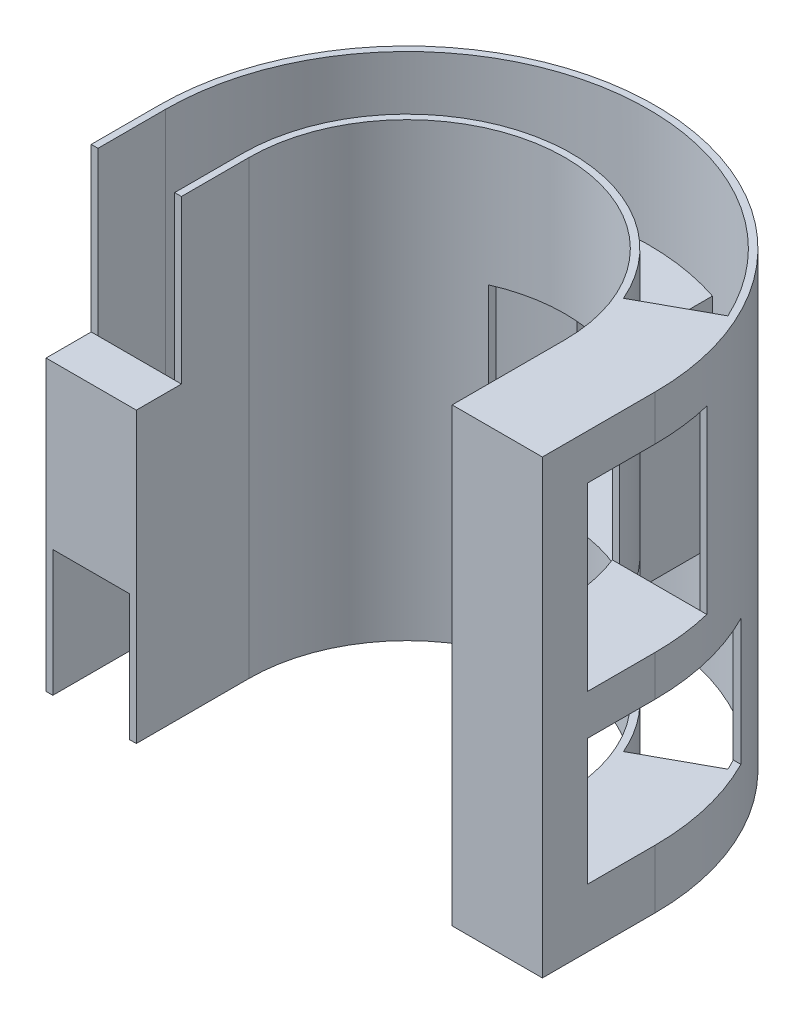
SolidWorks part; units mm, degrees
ref_plane "Front Plane" through (0, 0, 0) normal (0, 0, 1) x (1, 0, 0)
ref_plane "Top Plane" through (0, 0, 0) normal (0, 1, 0) x (1, 0, 0)
ref_plane "Right Plane" through (0, 0, 0) normal (1, 0, 0) x (0, 0, -1)
sketch "Sketch2" plane through (0, 0, 0) normal (0, 1, 0) x (1, 0, 0)
  circle A0 centre (0, 0) radius 27.5
  dimension "D1" = 55
extrude "Boss-Extrude1" add sketch "Sketch2" along normal blind 50 contours A0
sketch "Sketch3" plane through (0, 50, 0) normal (0, 1, 0) x (1, 0, 0)
  circle A0 centre (0, 0) radius 26.75
  dimension "D1" = 53.5
extrude "Cut-Extrude1" cut sketch "Sketch3" against normal through all
sketch "Sketch7" plane through (0, 50, 0) normal (0, 1, 0) x (1, 0, 0)
  circle A0 centre (0, 0) radius 18.25
  dimension "D1" = 36.5
extrude "Boss-Extrude3" add sketch "Sketch7" against normal blind 50 separate body
sketch "Sketch8" plane through (0, 50, 0) normal (0, 1, 0) x (1, 0, 0)
  circle A0 centre (0, 0) radius 17.5
  dimension "D1" = 35
extrude "Cut-Extrude3" cut sketch "Sketch8" against normal through all
sketch "Sketch9" plane through (0, 50, 0) normal (0, 1, 0) x (1, 0, 0)
  line L1 (-30.4577, 0) -> (29.5035, 0)
  line L2 (-30.4577, 0) -> (-30.4577, -28.5161)
  line L3 (-30.4577, -28.5161) -> (29.5035, -28.5161)
  line L4 (29.5035, 0) -> (29.5035, -28.5161)
extrude "Cut-Extrude4" cut sketch "Sketch9" against normal through all
sketch "Sketch10" plane through (0, 50, 0) normal (0, 1, 0) x (1, 0, 0)
  line L0 (-27.5, 0) -> (-27.5, -12.5)
  line L1 (-26.75, 0) -> (-27.5, 0) construction
  line L2 (-26.75, 0) -> (-26.75, -12.5)
  line L3 (-26.75, -12.5) -> (-27.5, -12.5)
  line L4 (-27.5, 0) -> (-26.75, 0)
  line L10 (-18.25, 0) -> (-17.5, 0)
  line L11 (-17.5, 0) -> (-18.25, 0) construction
  line L12 (-17.5, 0) -> (-17.5, -12.5)
  line L13 (-17.5, -12.5) -> (-18.25, -12.5)
  line L14 (-18.25, -12.5) -> (-18.25, 0)
  line L15 (17.5, 0) -> (18.25, 0)
  line L16 (18.25, 0) -> (18.25, -12.5)
  line L17 (18.25, -12.5) -> (17.5, -12.5)
  line L18 (17.5, -12.5) -> (17.5, 0)
  line L19 (27.5, 0) -> (26.75, 0)
  line L20 (26.75, 0) -> (26.75, -12.5)
  line L21 (26.75, -12.5) -> (27.5, -12.5)
  line L22 (27.5, -12.5) -> (27.5, 0)
  arc A0 (27.5, 0) -> (-27.5, 0) centre (0, 0) ccw construction
  arc A2 (17.5, 0) -> (-17.5, 0) centre (0, 0) ccw construction
  arc A3 (18.25, 0) -> (-18.25, 0) centre (0, 0) ccw construction
  dimension "D1" = 12.5
  dimension "D2" = 12.5
  dimension "D3" = 12.5
  dimension "D4" = 12.5
extrude "Boss-Extrude4" add sketch "Sketch10" against normal blind 50
sketch "Sketch11" plane through (0, 50, 0) normal (0, 1, 0) x (1, 0, 0)
  line L16 (18.25, -12.5) -> (18.25, 0) construction
  line L17 (16.7607, 7.2208) -> (24.2364, 11.3207)
  line L18 (18.25, 0) -> (18.25, -12.5)
  line L19 (18.25, -12.5) -> (26.75, -12.5)
  line L20 (26.75, -12.5) -> (26.75, 0)
  arc A4 (18.25, 0) -> (16.7607, 7.2208) centre (0, 0) ccw
  arc A5 (18.25, 0) -> (-18.25, 0) centre (0, 0) ccw construction
  arc A6 (26.75, 0) -> (24.2364, 11.3207) centre (0, 0) ccw
extrude "Boss-Extrude5" add sketch "Sketch11" against normal blind 5
sketch "Sketch12" plane through (27.5, 0, 0) normal (1, 0, 0) x (0, 0, -1)
  line L0 (-7.5, 45) -> (-7.5, 25)
  line L1 (-7.5, 25) -> (6.5, 25)
  line L2 (6.5, 25) -> (6.5, 45)
  line L3 (6.5, 45) -> (-7.5, 45)
  line L4 (-12.5, 0) -> (-12.5, 50) construction
  line L5 (27.5, 50) -> (0, 50) construction
  line L6 (-7.5, 20.5) -> (-7.5, 6.5)
  line L7 (-7.5, 6.5) -> (12.5, 6.5)
  line L8 (12.5, 6.5) -> (12.5, 20.5)
  line L9 (12.5, 20.5) -> (-7.5, 20.5)
  line L10 (-12.5, 0) -> (0, 0) construction
  dimension "D1" = 20
  dimension "D2" = 14
  dimension "D3" = 5
  dimension "D4" = 5
  dimension "D5" = 14
  dimension "D6" = 20
  dimension "D7" = 6.5
sketch "Sketch13" plane through (0, 0, 0) normal (0, -1, 0) x (1, 0, 0)
  line L0 (24.2364, -11.3207) -> (16.7607, -7.2208) construction
  line L1 (18.25, 0) -> (18.25, 12.5)
  line L2 (18.25, 12.5) -> (26.75, 12.5)
  line L3 (26.75, 12.5) -> (26.75, 0)
  line L4 (16.7607, -7.2208) -> (24.2364, -11.3207)
  arc A0 (18.25, 0) -> (16.7607, -7.2208) centre (0, 0) cw
  arc A3 (24.2364, -11.3207) -> (26.75, 0) centre (0, 0) ccw
  arc A4 (-26.75, 0) -> (26.75, 0) centre (0, 0) ccw construction
extrude "Boss-Extrude6" add sketch "Sketch13" against normal blind 6.5
extrude "Cut-Extrude6" cut sketch "Sketch12" against normal blind 15
sketch "Sketch14" plane through (0, 0, 12.5) normal (0, 0, 1) x (1, 0, 0)
  line L0 (7, 35) -> (7, 15)
  line L1 (7, 15) -> (-7, 15)
  line L2 (-7, 15) -> (-7, 35)
  line L3 (-7, 35) -> (7, 35)
  line L4 (17.5, 50) -> (-17.5, 50) construction
  dimension "D1" = 7
  dimension "D2" = 14
  dimension "D3" = 20
  dimension "D4" = 15
extrude "Cut-Extrude7" cut sketch "Sketch14" against normal blind 45
sketch "Sketch15" plane through (-27.5, 0, 0) normal (-1, 0, 0) x (0, 0, 1)
  line L0 (0, 0) -> (12.5, 0) construction
  line L1 (7.5, 54.2356) -> (24.1059, 54.2356)
  line L2 (7.5, 54.2356) -> (7.5, 32)
  line L3 (7.5, 32) -> (24.1059, 32)
  line L4 (24.1059, 54.2356) -> (24.1059, 32)
  line L5 (12.5, 0) -> (12.5, 50) construction
  dimension "D1" = 32
  dimension "D2" = 5
extrude "Cut-Extrude8" cut sketch "Sketch15" against normal blind 15
sketch "Sketch17" plane through (0, 25, 0) normal (0, 1, 0) x (1, 0, 0)
  line L0 (16.2481, 6.5) -> (17.0532, 6.5) construction
  line L1 (25.9483, 6.5) -> (26.7208, 6.5) construction
  line L2 (26.7208, 6.5) -> (17.0532, 6.5)
  line L3 (27.5, 0) -> (27.5, -7.5)
  line L4 (27.5, -7.5) -> (18.25, -7.5)
  line L5 (18.25, -7.5) -> (18.25, 0)
  arc A0 (18.25, 0) -> (17.0532, 6.5) centre (0, 0) ccw
  arc A1 (27.5, 0) -> (26.7208, 6.5) centre (0, 0) ccw
extrude "Boss-Extrude8" add sketch "Sketch17" against normal blind 4.5
sketch "Sketch18" plane through (0, 35, 0) normal (0, -1, 0) x (1, 0, 0)
  line L0 (7, -26.5942) -> (7, -25.8179) construction
  line L1 (-7, -16.8542) -> (-7, -25.8179)
  line L2 (7, -16.8542) -> (7, -25.8179)
  arc A0 (-7, -16.8542) -> (7, -16.8542) centre (0, 0) ccw
  arc A1 (-7, -16.8542) -> (7, -16.8542) centre (0, 0) ccw construction
  arc A2 (-7, -25.8179) -> (7, -25.8179) centre (0, 0) ccw
extrude "Boss-Extrude9" add sketch "Sketch18" against normal blind 2
sketch "Sketch19" plane through (0, 15, 0) normal (0, 1, 0) x (1, 0, 0)
  line L0 (7, 16.8542) -> (7, 16.039) construction
  line L1 (7, 25.8179) -> (7, 16.8542)
  line L2 (-7, 25.8179) -> (-7, 16.8542)
  arc A0 (-7, 16.8542) -> (7, 16.8542) centre (0, 0) cw
  arc A1 (-7, 25.8179) -> (7, 25.8179) centre (0, 0) cw
  arc A2 (7, 25.8179) -> (-7, 25.8179) centre (0, 0) ccw construction
extrude "Boss-Extrude10" add sketch "Sketch19" against normal blind 2
sketch "Sketch24" plane through (0, 37, 0) normal (0, 1, 0) x (1, 0, 0)
  line L0 (8.4749, 25.372) -> (8.4749, 16.1629)
  line L1 (7, 25.8179) -> (7, 16.8542)
  arc A1 (7, 25.8179) -> (8.4749, 25.372) centre (0, 0) cw
  arc A3 (7, 16.8542) -> (8.4749, 16.1629) centre (0, 0) cw
extrude "Boss-Extrude15" add sketch "Sketch24" against normal blind 24
sketch "Sketch25" plane through (27.5, 0, 0) normal (1, 0, 0) x (0, 0, -1)
  line L1 (-12.5, 0) -> (-12.5, 50) construction
  line L2 (-7.5, 45) -> (-12.5, 45)
  line L3 (-7.5, 25) -> (-7.5, 45)
  line L4 (-12.5, 45) -> (-12.5, 25)
  line L5 (-7.5, 25) -> (-7.5, 20.5)
  line L6 (-7.5, 20.5) -> (-12.5, 20.5)
  line L7 (-12.5, 20.5) -> (-12.5, 25)
extrude "Boss-Extrude17" add sketch "Sketch25" against normal blind 10
sketch "Sketch26" plane through (-27.5, 0, 0) normal (-1, 0, 0) x (0, 0, 1)
  line L0 (12.5, 32) -> (7.5, 32)
  line L1 (7.5, 32) -> (7.5, 14)
  line L2 (7.5, 14) -> (12.5, 14)
  line L3 (12.5, 0) -> (12.5, 32) construction
  line L4 (12.5, 14) -> (12.5, 32)
  dimension "D1" = 18
extrude "Boss-Extrude18" add sketch "Sketch26" against normal blind 10
sketch "Sketch27" plane through (0, 0, 12.5) normal (0, 0, 1) x (1, 0, 0)
  line L1 (18.25, 20.5) -> (26.75, 20.5)
  line L2 (18.25, 20.5) -> (18.25, 6.5)
  line L3 (18.25, 6.5) -> (26.75, 6.5)
  line L4 (26.75, 20.5) -> (26.75, 6.5)
extrude "Boss-Extrude19" add sketch "Sketch27" against normal blind 5
